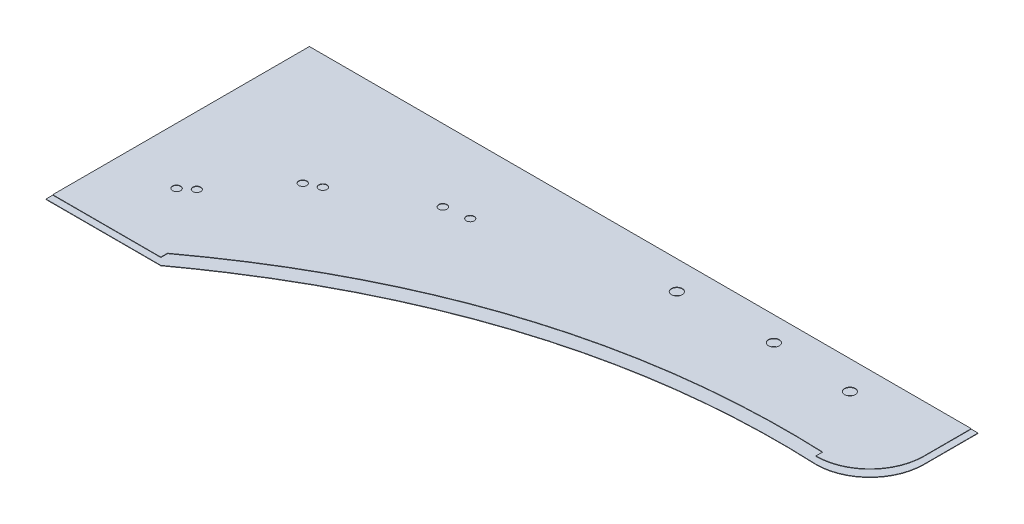
SolidWorks part; units mm, degrees
material "Thornel Mat VMA"
ref_plane "Płaszczyzna XY" through (0, 0, 0) normal (0, 0, 1) x (1, 0, 0)
ref_plane "Płaszczyzna XZ" through (0, 0, 0) normal (0, 1, 0) x (1, 0, 0)
ref_plane "Płaszczyzna YZ" through (0, 0, 0) normal (1, 0, 0) x (0, 0, -1)
sketch "Szkic1" plane through (0, 705, 0) normal (0, 1, 0) x (1, 0, 0)
  line L6 (-66.203, -312.6816) -> (-66.203, -317.6816)
  line L7 (-26.203, -277.6816) -> (-26.203, -242.6816)
  line L8 (-26.203, -242.6816) -> (-516.203, -242.6816)
  line L9 (-516.203, -242.6816) -> (-516.203, -432.6816)
  line L10 (-516.203, -432.6816) -> (-436.203, -432.6816)
  line L11 (-436.203, -432.6816) -> (-436.203, -427.6816)
  line L12 (-66.203, -312.6816) -> (-66.203, -317.6816)
  line L13 (-26.203, -277.6816) -> (-26.203, -242.6816)
  line L14 (-26.203, -242.6816) -> (-516.203, -242.6816)
  line L15 (-516.203, -242.6816) -> (-516.203, -432.6816)
  line L16 (-516.203, -432.6816) -> (-436.203, -432.6816)
  line L17 (-436.203, -432.6816) -> (-436.203, -427.6816)
  arc A1 (-66.203, -317.6816) -> (-26.203, -277.6816) centre (-66.203, -277.6816) ccw
  arc A2 (-66.203, -317.6816) -> (-26.203, -277.6816) centre (-66.203, -277.6816) ccw
  parabola Q1 (-436.203, -427.6816) -> (-66.203, -312.6816) focus (-166.764, -594.9277) apex (-236.0841, -330.2641)
  parabola Q2 (-436.203, -427.6816) -> (-66.203, -312.6816) focus (-166.764, -594.9277) apex (-236.0841, -330.2641)
  dimension "D1" = 0
extrude "Dodanie-wyciągnięcie1" add sketch "Szkic1" along normal blind 0.3
sketch "Szkic2" plane through (0, 700, 0) normal (0, -1, 0) x (1, 0, 0)
  line L4 (-521.203, 432.6816) -> (-521.203, 237.6816)
  line L5 (-521.203, 237.6816) -> (-26.203, 237.6816)
  line L6 (-26.203, 237.6816) -> (-26.203, 277.6816)
  line L7 (-436.203, 432.6816) -> (-521.203, 432.6816)
  line L8 (-521.203, 432.6816) -> (-521.203, 237.6816)
  line L9 (-521.203, 237.6816) -> (-26.203, 237.6816)
  line L10 (-26.203, 237.6816) -> (-26.203, 277.6816)
  line L11 (-436.203, 432.6816) -> (-521.203, 432.6816)
  arc A1 (-26.203, 277.6816) -> (-66.203, 317.6816) centre (-66.203, 277.6816) ccw
  arc A2 (-26.203, 277.6816) -> (-66.203, 317.6816) centre (-66.203, 277.6816) ccw
  parabola Q1 (-66.203, 317.6816) -> (-436.203, 432.6816) focus (-154.3189, 595.6573) apex (-212.0102, 329.5368)
  parabola Q2 (-66.203, 317.6816) -> (-436.203, 432.6816) focus (-154.3189, 595.6573) apex (-212.0102, 329.5368)
  dimension "D1" = 0
extrude "Dodanie-wyciągnięcie2" add sketch "Szkic2" along normal blind 0.3 separate body
sketch "Szkic3" plane through (0, 699.7, 0) normal (0, -1, 0) x (1, 0, 0)
  circle A0 centre (-94.9095, 263.8022) radius 4
  circle A1 centre (-154.3447, 260.6438) radius 4
  circle A2 centre (-223.0248, 263.8022) radius 4
  circle A3 centre (-346.3728, 293.4293) radius 2.9446
  circle A4 centre (-364.0177, 296.0486) radius 3.0206
  circle A5 centre (-421.0828, 327.8098) radius 3.0122
  circle A6 centre (-431.0134, 332.7713) radius 2.9697
  circle A7 centre (-466.3178, 375.9237) radius 2.9264
  circle A8 centre (-474.4492, 382.7937) radius 3.0223
extrude "Wytnij-wyciągnięcie1" cut sketch "Szkic3" against normal blind 20
